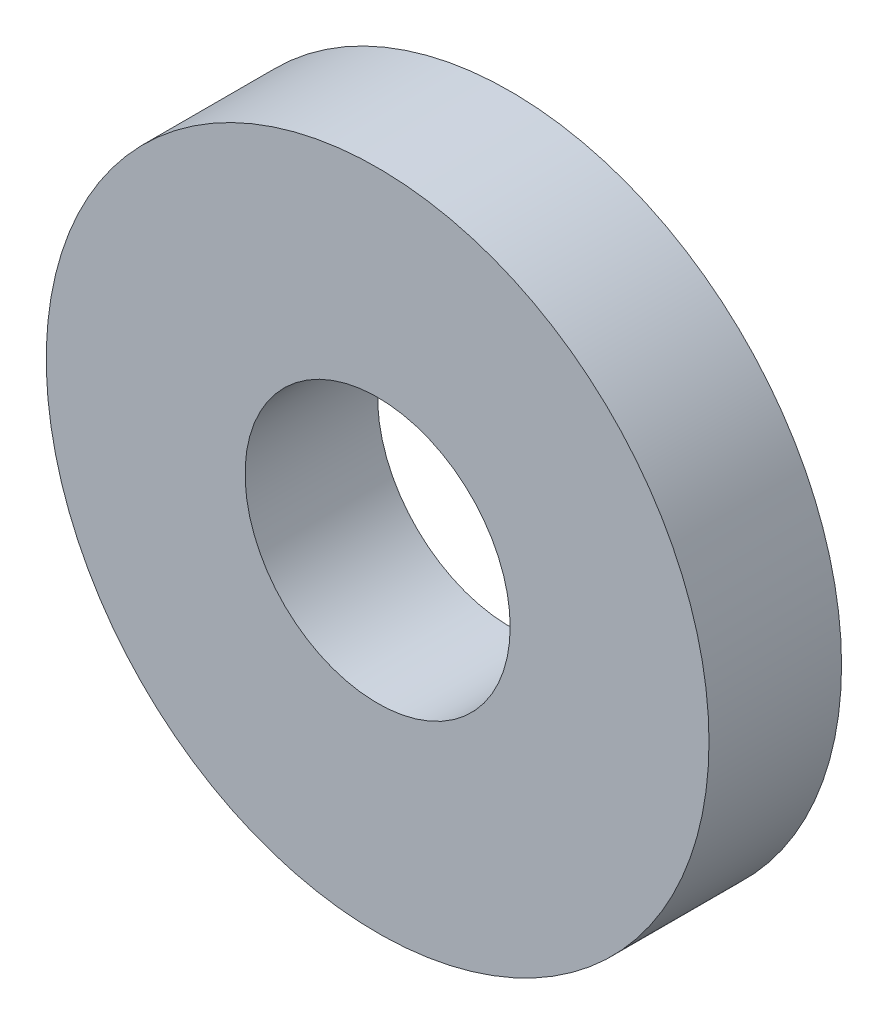
SolidWorks part; units mm, degrees
ref_plane "Front Plane" through (0, 0, 0) normal (0, 0, 1) x (1, 0, 0)
ref_plane "Top Plane" through (0, 0, 0) normal (0, 1, 0) x (1, 0, 0)
ref_plane "Right Plane" through (0, 0, 0) normal (1, 0, 0) x (0, 0, -1)
sketch "Sketch1" plane through (0, 0, 0) normal (0, 0, 1) x (1, 0, 0)
  circle A0 centre (0, 0) radius 12.5
  circle A1 centre (0, 0) radius 5
  dimension "D1" = 25
  dimension "D2" = 10
extrude "Boss-Extrude1" add sketch "Sketch1" along normal blind 5
